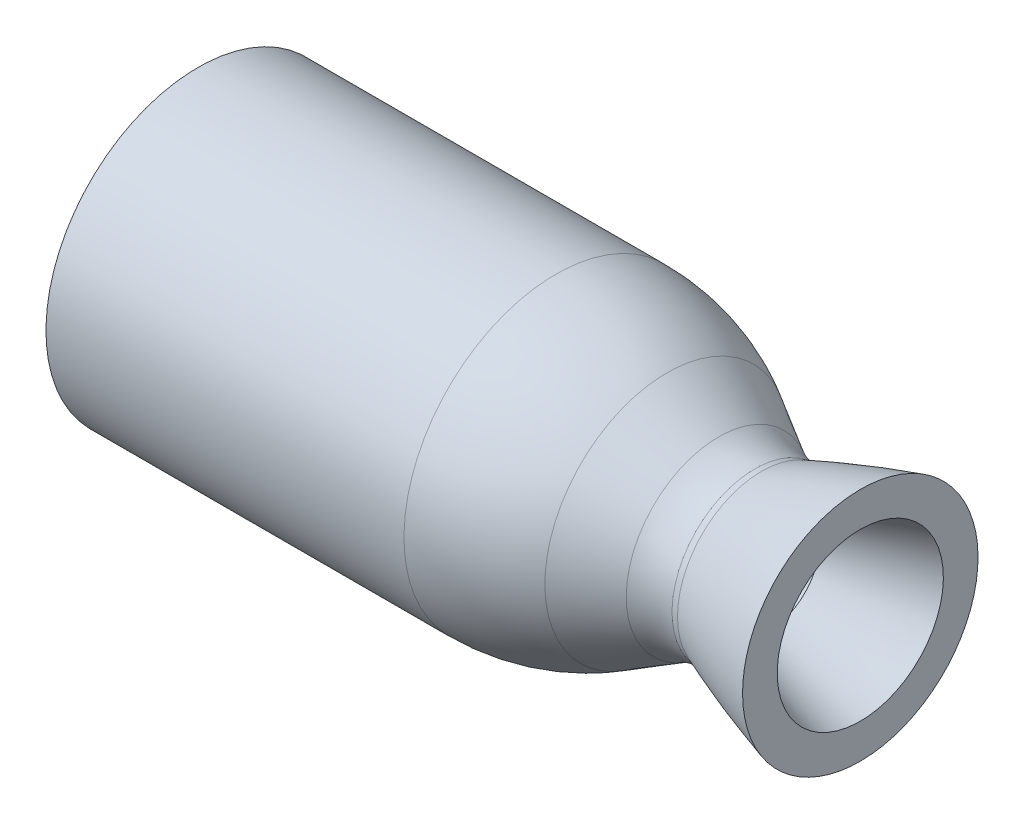
SolidWorks part; units mm, degrees
ref_plane "Front Plane" through (0, 0, 0) normal (0, 0, 1) x (1, 0, 0)
ref_plane "Top Plane" through (0, 0, 0) normal (0, 1, 0) x (1, 0, 0)
ref_plane "Right Plane" through (0, 0, 0) normal (1, 0, 0) x (0, 0, -1)
sketch "Model" plane through (0, 0, 0) normal (0, 0, 1) x (1, 0, 0)
  line L0 (37.9853, 43.0587) -> (169.3033, 43.0587)
  line L1 (0, -43.0587) -> (169.3033, -43.0587) construction
  line L2 (210.0626, 32.1372) -> (228.979, 21.2158)
  line L3 (210.0626, -32.1372) -> (228.979, -21.2158) construction
  line L4 (0, 0) -> (296.8091, 0) construction
  line L5 (296.8091, 34.6444) -> (297.9091, 34.6444) construction
  line L6 (296.8091, 34.6444) -> (297.8796, 34.8976)
  line L7 (261.1382, 24.5966) -> (244.6972, 18.1335) construction
  line L8 (37.9853, 55.7587) -> (169.3033, 55.7587)
  line L9 (210.0626, 44.8372) -> (228.979, 33.9158)
  line L10 (37.9853, 55.7587) -> (37.9853, 43.0587)
  line L11 (296.8091, 47.3444) -> (297.8796, 34.8976)
  line L12 (244.6972, 30.8335) -> (242.2283, 30.3657)
  arc A0 (210.0626, 32.1372) -> (169.3033, 43.0587) centre (169.3033, -38.4599) ccw
  arc A1 (169.3033, -43.0587) -> (210.0626, -32.1372) centre (169.3033, 38.4599) ccw construction
  arc A2 (228.979, 21.2158) -> (242.2283, 17.6657) centre (242.2283, 44.1643) ccw
  arc A3 (242.2283, -17.6657) -> (228.979, -21.2158) centre (242.2283, -44.1642) ccw construction
  arc A4 (242.2283, 17.6657) -> (244.6972, 18.1335) centre (242.2283, 24.414) ccw
  arc A5 (244.6972, -18.1335) -> (242.2283, -17.6657) centre (242.2283, -24.414) ccw construction
  arc A6 (210.0626, 44.8372) -> (169.3033, 55.7587) centre (169.3033, -25.7599) ccw
  arc A7 (228.979, 33.9158) -> (242.2283, 30.3657) centre (242.2283, 56.8643) ccw
  spline S0 degree 2 poles (244.6972, 18.1335) (271.4171, 28.6373) (296.8091, 34.6444) knots 0 0 0 1 1 1
  spline S1 degree 2 poles (244.6972, -18.1335) (271.4171, -28.6373) (296.8091, -34.6444) knots 0 0 0 1 1 1 construction
  spline S2 degree 2 poles (244.6972, 30.8335) (271.4171, 41.3373) (296.8091, 47.3444) knots 0 0 0 1 1 1
  dimension "D6" = 81.5186
  dimension "D7" = 26.4986
  dimension "D11" = 6.7483
  dimension "D1" = 86.1173
  dimension "D2" = 35.3314
  dimension "D3" = 169.3033
  dimension "D4" = 131.318
  dimension "D8" = 30
  dimension "D9" = 69.2887
  dimension "D10" = 166.69
  dimension "D12" = 21.46
  dimension "D13" = 2
revolve "Revolve2" add sketch "Model" angle 360 about L4
sketch "Sketch1" plane through (0, 0, 0) normal (0, 0, 1) x (1, 0, 0)
  line L8 (0, 0) -> (296.8091, 0) construction
  line L9 (0, 0) -> (296.8091, 0) construction
  line L10 (280.911, 0) -> (280.911, 30.48) construction
  line L12 (280.911, 0) -> (318.7866, 0)
  line L13 (280.911, 0) -> (280.911, 61.5874)
  line L14 (280.911, 61.5874) -> (318.7866, 61.5874)
  line L15 (318.7866, 0) -> (318.7866, 61.5874)
  parabola Q3 (244.6972, 18.1335) -> (296.8091, 34.6444) focus (395.9771, -71.429) apex (426.9698, 33.5163) construction
  parabola Q4 (244.6972, 18.1335) -> (296.8091, 34.6444) focus (395.9771, -71.429) apex (426.9698, 33.5163) construction
  dimension "D1" = 30.48
revolve "Cut-Revolve1" cut sketch "Sketch1" angle 360 about L12
sketch "Sketch2" plane through (0, 0, 0) normal (0, 0, 1) x (1, 0, 0)
  line L1 (0, 0) -> (307.9511, 0)
  line L2 (0, 0) -> (0, 19.05)
  line L3 (0, 19.05) -> (307.9511, 19.05)
  line L4 (307.9511, 0) -> (307.9511, 19.05)
  dimension "D1" = 19.05
revolve "Cut-Revolve2" cut sketch "Sketch2" angle 360 about L1
sketch "point" plane through (280.911, 0, 0) normal (1, 0, 0) x (0, 0, -1)
  point P0 (0, 0)
